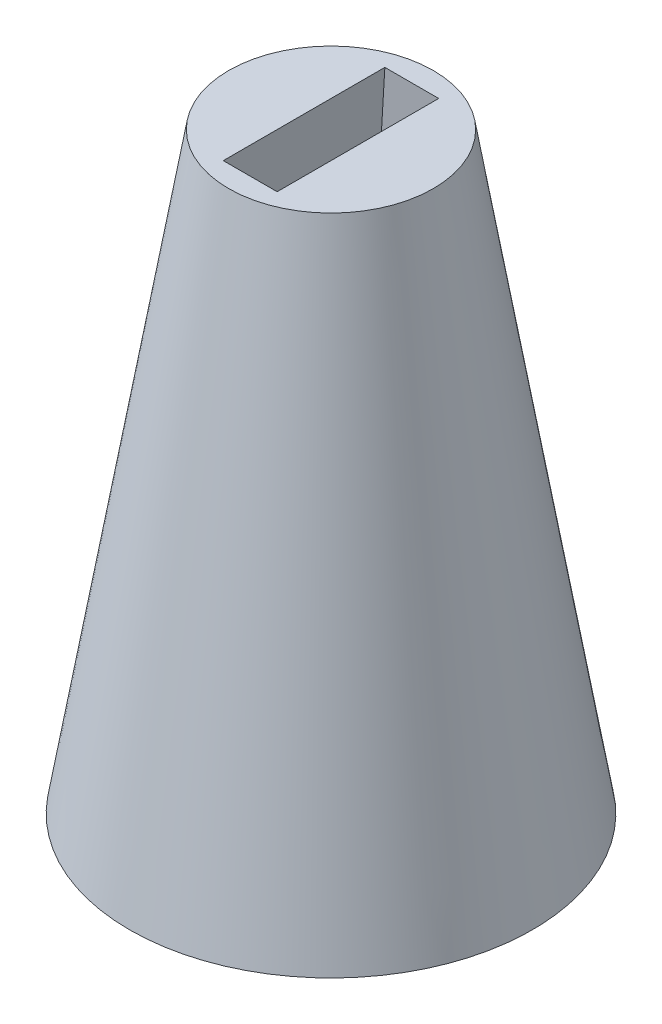
SolidWorks part; units mm, degrees
other "마크업1"
sketch "스케치3" plane through (16.5751, -0.0001, 16.5751) normal (0.202, -0.0111, 0.9793) x (0.9775, -0.0591, -0.2023)
ref_plane "정면" through (0, 0, 0) normal (0, 0, 1) x (1, 0, 0)
ref_plane "윗면" through (0, 0, 0) normal (0, 1, 0) x (1, 0, 0)
ref_plane "우측면" through (0, 0, 0) normal (1, 0, 0) x (0, 0, -1)
sketch "스케치1" plane through (0, 0, 0) normal (0, 1, 0) x (1, 0, 0)
  circle A0 centre (0, 0) radius 18.7
  dimension "38.9" = 37.4
ref_plane "평면1" through (0, 55, 0) normal (0, 1, 0) x (1, 0, 0)
sketch "스케치2" plane through (0, 55, 0) normal (0, 1, 0) x (1, 0, 0)
  circle A0 centre (0, 0) radius 9.5
  dimension "D1" = 19
sketch3d "3D스케치1"
  line L0 (9.5, 55, 0) -> (18.7, 0, 0) construction
  circle A1 centre (0, 55, 0) radius 9.5 construction
  circle A2 centre (0, 0, 0) radius 18.7 construction
  point P4 (0, 64.5, 0)
  point P7 (0, 18.7, 0)
loft "로프트1" add profiles "스케치2", "스케치1"
sketch "스케치5" plane through (0, 0, 0) normal (0, -1, 0) x (1, 0, 0)
  line L1 (-5.75, 9.5) -> (5.75, 9.5)
  line L2 (-5.75, 9.5) -> (-5.75, -9.5)
  line L3 (-5.75, -9.5) -> (5.75, -9.5)
  line L4 (5.75, 9.5) -> (5.75, -9.5)
  line L5 (-5.75, 9.5) -> (5.75, -9.5) construction
  line L6 (-5.75, -9.5) -> (5.75, 9.5) construction
  point P0 (0, 0)
  dimension "D1" = 19
  dimension "D2" = 11.5
sketch "스케치6" plane through (0, 55, 0) normal (0, 1, 0) x (1, 0, 0)
  line L6 (-2.5, 7.5) -> (2.5, 7.5)
  line L7 (-2.5, 7.5) -> (-2.5, -7.5)
  line L8 (-2.5, -7.5) -> (2.5, -7.5)
  line L9 (2.5, 7.5) -> (2.5, -7.5)
  line L10 (-2.5, 7.5) -> (2.5, -7.5) construction
  line L11 (-2.5, -7.5) -> (2.5, 7.5) construction
  point P0 (0, 0)
  dimension "D1" = 15
  dimension "D2" = 5
extrude "컷-돌출1" cut sketch "스케치5" against normal blind 32
sketch "스케치9" plane through (0, 32, 0) normal (0, -1, 0) x (1, 0, 0)
  line L4 (5.75, -9.5) -> (5.75, 9.5)
  line L5 (5.75, 9.5) -> (-5.75, 9.5)
  line L6 (-5.75, 9.5) -> (-5.75, -9.5)
  line L7 (-5.75, -9.5) -> (5.75, -9.5)
  line L8 (5.75, -9.5) -> (5.75, 9.5)
  line L9 (5.75, 9.5) -> (-5.75, 9.5)
  line L10 (-5.75, 9.5) -> (-5.75, -9.5)
  line L11 (-5.75, -9.5) -> (5.75, -9.5)
  dimension "D1" = 0
loft "컷-로프트2" cut profiles "스케치9", "스케치6"
